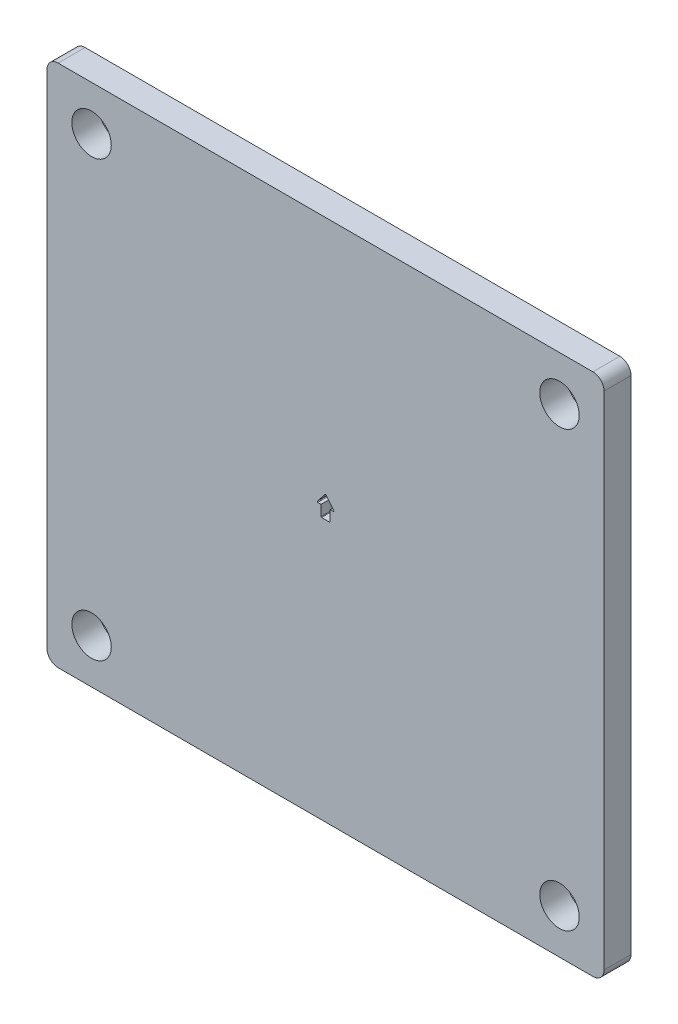
SolidWorks part; units mm, degrees
material "Acrylic (Medium-high impact)"
ref_plane "Front Plane" through (0, 0, 0) normal (0, 0, 1) x (1, 0, 0)
ref_plane "Top Plane" through (0, 0, 0) normal (0, 1, 0) x (1, 0, 0)
ref_plane "Right Plane" through (0, 0, 0) normal (1, 0, 0) x (0, 0, -1)
sketch "Sketch1" plane through (0, 0, 0) normal (0, 0, 1) x (1, 0, 0)
  line L0 (6.35, 35.56) -> (6.35, 10.16) construction
  line L1 (0, 0) -> (63.5, 0)
  line L2 (0, 0) -> (0, 59.69)
  line L3 (0, 59.69) -> (63.5, 59.69)
  line L4 (63.5, 0) -> (63.5, 59.69)
  line L5 (6.35, 10.16) -> (57.15, 10.16) construction
  line L6 (57.15, 10.16) -> (57.15, 35.56) construction
  line L7 (57.15, 35.56) -> (6.35, 35.56) construction
  line L8 (31.75, 0) -> (31.75, 10.16) construction
  point P11 (5.08, 54.61)
  point P12 (58.42, 54.61)
  point P13 (58.42, 5.08)
  point P14 (5.08, 5.08)
  dimension "D1" = 5.08
  dimension "D2" = 5.08
  dimension "D3" = 25.4
  dimension "D4" = 50.8
  dimension "D5" = 5.08
  dimension "D6" = 5.08
  dimension "D7" = 5.08
  dimension "D8" = 19.05
  dimension "D9" = 6.35
extrude "Boss-Extrude1" add sketch "Sketch1" along normal blind 3.0734
fillet "Fillet1" radius 1.27 4 edges at (0, 0, 1.5367) (63.5, 0, 1.5367) (63.5, 59.69, 1.5367) (0, 59.69, 1.5367)
sketch "Sketch6" plane through (0, 0, 3.0734) normal (0, 0, 1) x (1, 0, 0)
  line L0 (31.75, 59.69) -> (31.75, 22.225) construction
  line L1 (6.35, 9.525) -> (57.15, 9.525) construction
  line L2 (6.35, 9.525) -> (6.35, 22.225) construction
  line L3 (6.35, 22.225) -> (57.15, 22.225) construction
  line L4 (57.15, 9.525) -> (57.15, 22.225) construction
  line L5 (62.23, 59.69) -> (1.27, 59.69) construction
  line L6 (1.27, 0) -> (62.23, 0) construction
  dimension "D1" = 50.8
  dimension "D2" = 12.7
  dimension "D3" = 9.525
hole_wizard "#8 Clearance Hole1" positions "Sketch5" profile "Sketch4" hole size "#8" standard "ANSI Inch" end condition through all
sketch "Sketch5" plane through (0, 0, 3.0734) normal (0, 0, 1) x (1, 0, 0)
  line L5 (31.75, 59.69) -> (31.75, 0) construction
  line L6 (62.23, 59.69) -> (1.27, 59.69) construction
  line L7 (1.27, 0) -> (62.23, 0) construction
  line L10 (0, 29.845) -> (63.5, 29.845) construction
  line L11 (0, 58.42) -> (0, 1.27) construction
  line L12 (63.5, 1.27) -> (63.5, 58.42) construction
  point P78 (5.08, 54.61)
  point P81 (58.42, 54.61)
  point P84 (58.42, 5.08)
  point P87 (5.08, 5.08)
sketch "Sketch4" plane through (5.08, 54.61, 3.0734) normal (1, 0, 0) x (0, -1, 0)
  line L0 (0, 0) -> (0, 3.0734)
  line L1 (0, 3.0734) -> (2.2479, 3.0734)
  line L2 (2.2479, 3.0734) -> (2.2479, 0)
  line L5 (2.2479, 0) -> (0, 0)
  line L11 (0, -6.35) -> (0, 107.95) construction
  dimension "Thru Hole Dia." = 4.4958
  dimension "Thru Hole Depth" = 3.0734
sketch "Sketch7" plane through (0, 0, 3.0734) normal (0, 0, 1) x (1, 0, 0)
  line L0 (0, 29.845) -> (63.5, 29.845) construction
  line L1 (0, 58.42) -> (0, 1.27) construction
  line L2 (63.5, 1.27) -> (63.5, 58.42) construction
  line L3 (31.75, 59.69) -> (31.75, 0) construction
  line L4 (62.23, 59.69) -> (1.27, 59.69) construction
  line L5 (1.27, 0) -> (62.23, 0) construction
  line L6 (31.242, 29.845) -> (31.242, 31.115)
  line L7 (31.242, 31.115) -> (30.734, 31.115)
  line L8 (30.734, 31.115) -> (31.75, 32.385)
  line L9 (31.242, 29.845) -> (32.258, 29.845)
  line L10 (32.258, 29.845) -> (32.258, 31.115)
  line L11 (32.258, 31.115) -> (32.766, 31.115)
  line L12 (32.766, 31.115) -> (31.75, 32.385)
  line L13 (31.75, 20.32) -> (54.3028, 20.32) construction
  point P18 (31.75, 29.845)
  dimension "D1" = 1.27
  dimension "D2" = 1.27
  dimension "D3" = 0.508
  dimension "D4" = 1.016
  dimension "D5" = 9.525
extrude "Cut-Extrude1" cut sketch "Sketch7" against normal through all
fillet "Fillet2" radius 0.0635 6 edges at (32.766, 31.115, 1.5367) (31.75, 32.385, 1.5367) (30.734, 31.115, 1.5367) (32.258, 29.845, 1.5367) (31.242, 29.845, 1.5367) (32.258, 31.115, 1.5367)
equation "\"pl\"=0.1"
